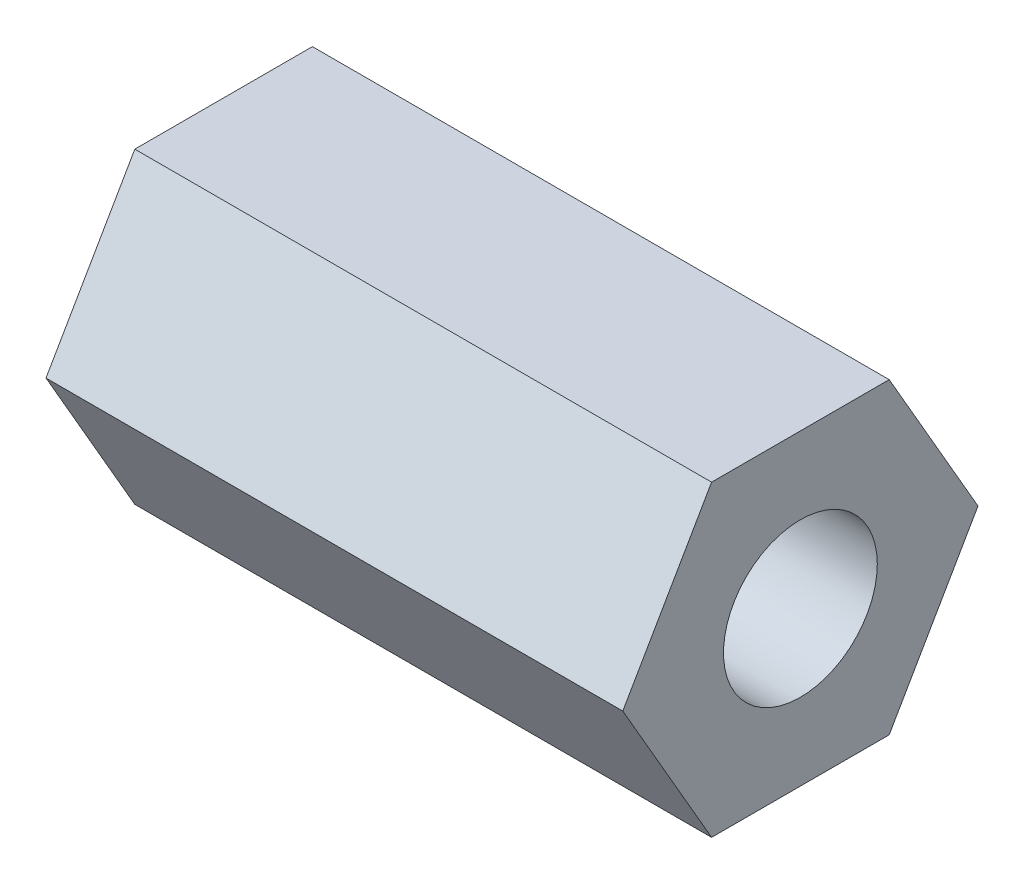
SolidWorks part; units mm, degrees
ref_plane "Front Plane" through (0, 0, 0) normal (0, 0, 1) x (1, 0, 0)
ref_plane "Top Plane" through (0, 0, 0) normal (0, 1, 0) x (1, 0, 0)
ref_plane "Right Plane" through (0, 0, 0) normal (1, 0, 0) x (0, 0, -1)
sketch "Sketch1" plane through (0, 0, 0) normal (1, 0, 0) x (0, 0, -1)
  line L1 (2.3094, -4) -> (4.6188, 0)
  line L2 (4.6188, 0) -> (2.3094, 4)
  line L3 (2.3094, 4) -> (-2.3094, 4)
  line L4 (-2.3094, 4) -> (-4.6188, 0)
  line L5 (-4.6188, 0) -> (-2.3094, -4)
  line L6 (-2.3094, -4) -> (2.3094, -4)
  circle A0 centre (0, 0) radius 4 construction
  circle A1 centre (0, 0) radius 2
  dimension "D1" = 8
  dimension "D2" = 4
extrude "Boss-Extrude1" add sketch "Sketch1" along normal blind 15
